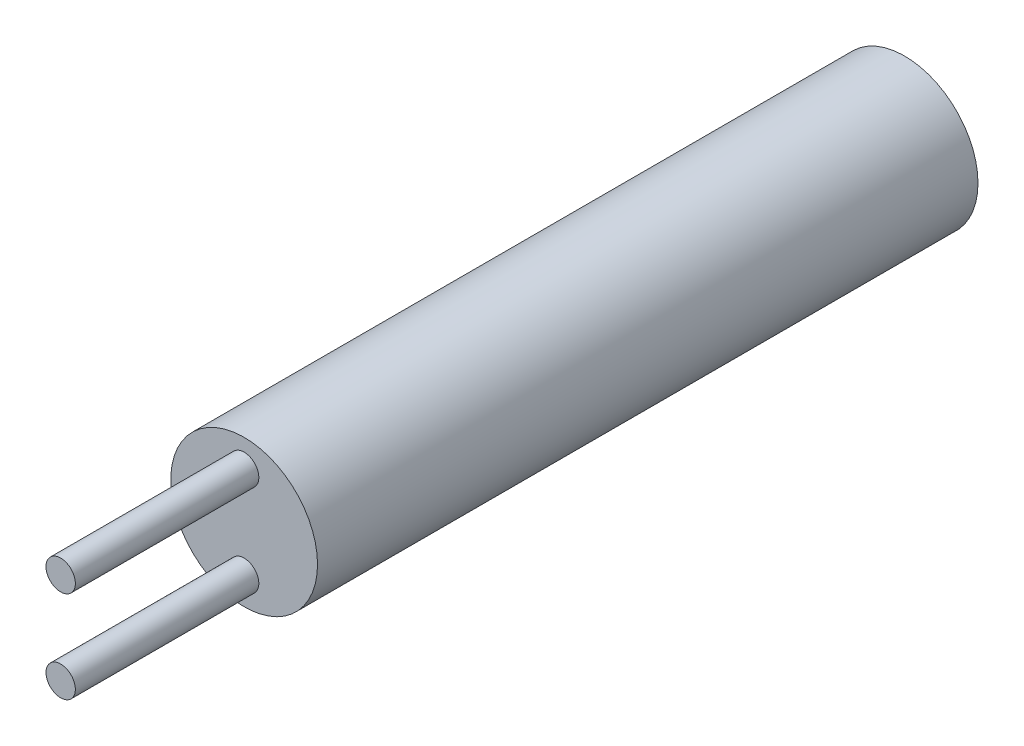
SolidWorks part; units mm, degrees
ref_plane "Front Plane" through (0, 0, 0) normal (0, 0, 1) x (1, 0, 0)
ref_plane "Top Plane" through (0, 0, 0) normal (0, 1, 0) x (1, 0, 0)
ref_plane "Right Plane" through (0, 0, 0) normal (1, 0, 0) x (0, 0, -1)
sketch "Sketch1" plane through (0, 0, 0) normal (0, 0, 1) x (1, 0, 0)
  circle A0 centre (0, 0) radius 2
  dimension "D1" = 4
extrude "Boss-Extrude1" add sketch "Sketch1" along normal blind 18
sketch "Sketch2" plane through (0, 0, 18) normal (0, 0, 1) x (1, 0, 0)
  line L0 (0, -2) -> (0, 2) construction
  line L1 (0, 0) -> (-2, 0) construction
  circle A0 centre (0, 0) radius 2 construction
  circle A1 centre (0, 1.25) radius 0.4
  circle A2 centre (0, -1.25) radius 0.4
  dimension "D1" = 2.5
  dimension "D2" = 0.8
extrude "Boss-Extrude2" add sketch "Sketch2" along normal blind 5
